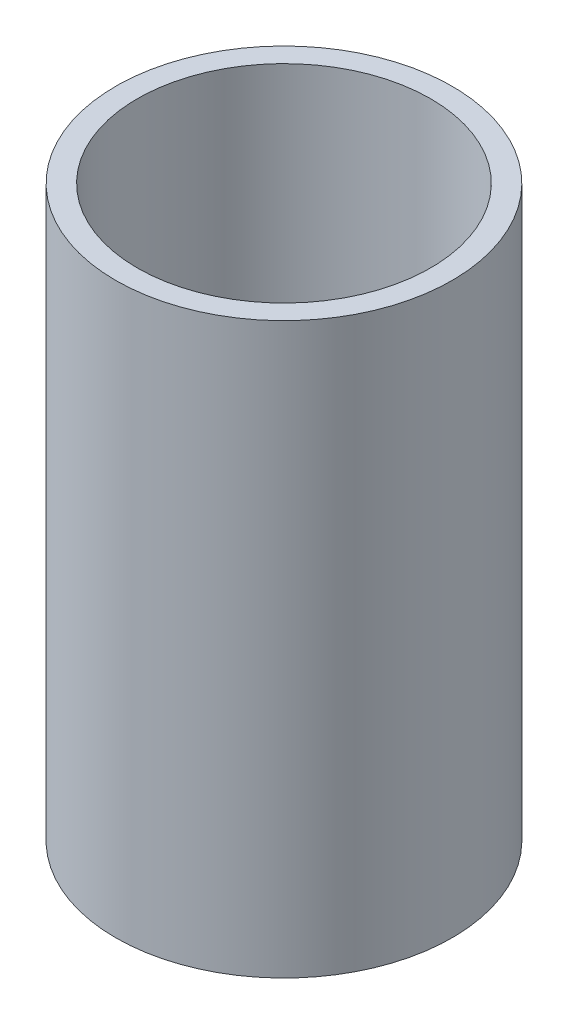
SolidWorks part; units mm, degrees
ref_plane "Front" through (0, 0, 0) normal (0, 0, 1) x (1, 0, 0)
ref_plane "Top" through (0, 0, 0) normal (0, 1, 0) x (1, 0, 0)
ref_plane "Right" through (0, 0, 0) normal (1, 0, 0) x (0, 0, -1)
sketch "Sketch2" plane through (0, 0, 0) normal (0, 1, 0) x (1, 0, 0)
  circle A0 centre (0, 0) radius 9.75
  circle A1 centre (0, 0) radius 8.5
  dimension "D1" = 17
  dimension "D2" = 19.5
extrude "Boss-Extrude1" add sketch "Sketch2" along normal blind 33
sketch "Sketch3" plane through (0, 0, 0) normal (0, 1, 0) x (1, 0, 0)
  circle A0 centre (0, 0) radius 8.5
  circle A1 centre (0, 0) radius 5
  dimension "D1" = 10
extrude "Boss-Extrude2" add sketch "Sketch3" along normal blind 2
